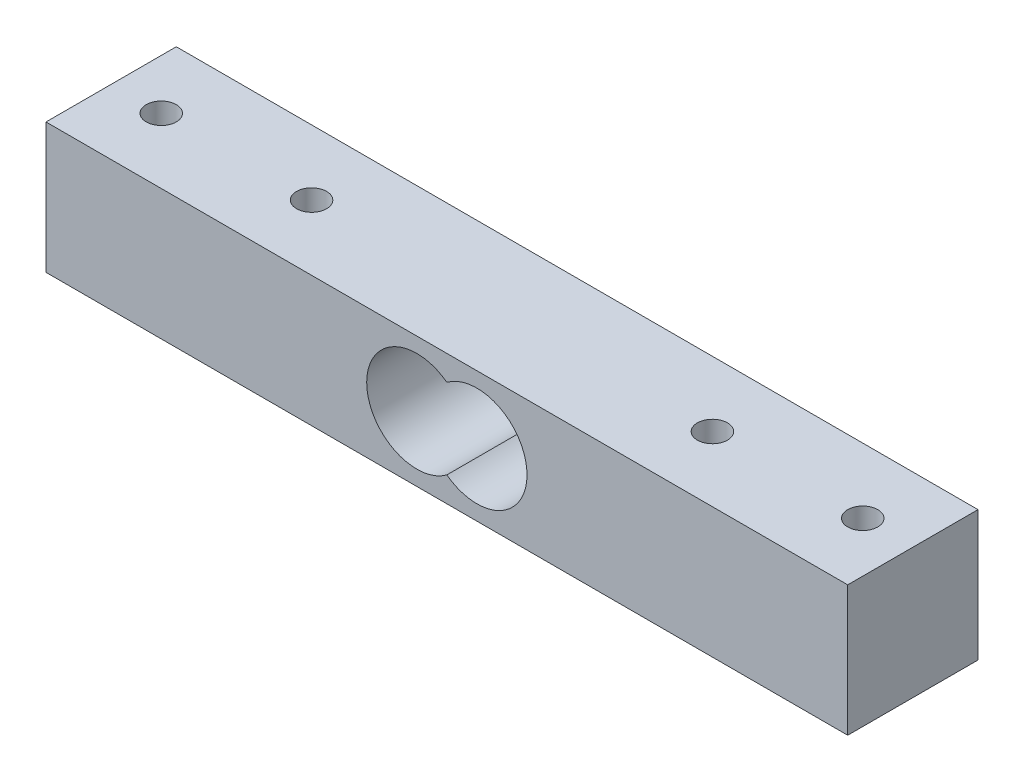
SolidWorks part; units mm, degrees
ref_plane "Front Plane" through (0, 0, 0) normal (0, 0, 1) x (1, 0, 0)
ref_plane "Top Plane" through (0, 0, 0) normal (0, 1, 0) x (1, 0, 0)
ref_plane "Right Plane" through (0, 0, 0) normal (1, 0, 0) x (0, 0, -1)
sketch "Sketch1" plane through (0, 0, 0) normal (0, 1, 0) x (1, 0, 0)
  line L1 (-40, -6.5) -> (40, -6.5)
  line L2 (-40, -6.5) -> (-40, 6.5)
  line L3 (-40, 6.5) -> (40, 6.5)
  line L4 (40, -6.5) -> (40, 6.5)
  line L5 (-40, -6.5) -> (40, 6.5) construction
  line L6 (-40, 6.5) -> (40, -6.5) construction
  point P0 (0, 0)
  dimension "D1" = 80
  dimension "D2" = 13
extrude "Boss-Extrude1" add sketch "Sketch1" along normal blind 13
sketch "Sketch3" plane through (0, 0, 0) normal (0, 0, 1) x (1, 0, 0)
  line L0 (0, 0) -> (0, 13) construction
  line L1 (-40, 13) -> (40, 13) construction
  line L2 (0, 6.5) -> (3, 6.5) construction
  arc A0 (0, 2.5) -> (0, 10.5) centre (3, 6.5) ccw
  arc A1 (0, 2.5) -> (0, 10.5) centre (-3, 6.5) cw
  dimension "D1" = 10
  dimension "D2" = 3
extrude "Cut-Extrude1" cut sketch "Sketch3" against normal through all both and the other way through all
sketch "Sketch4" plane through (0, 13, 0) normal (0, 1, 0) x (1, 0, 0)
  line L0 (0, 0) -> (0, 18.0911) construction
  line L1 (-35, 0) -> (-20, 0) construction
  line L2 (-20, 0) -> (20, 0) construction
  line L3 (-40, 6.5) -> (-40, -6.5) construction
  line L4 (35, 0) -> (20, 0) construction
  circle A0 centre (-35, 0) radius 1.5
  circle A1 centre (-20, 0) radius 1.5
  circle A2 centre (20, 0) radius 1.5
  circle A3 centre (35, 0) radius 1.5
  dimension "D3" = 3
  dimension "D1" = 15
  dimension "D2" = 5
extrude "Cut-Extrude2" cut sketch "Sketch4" against normal up to next
